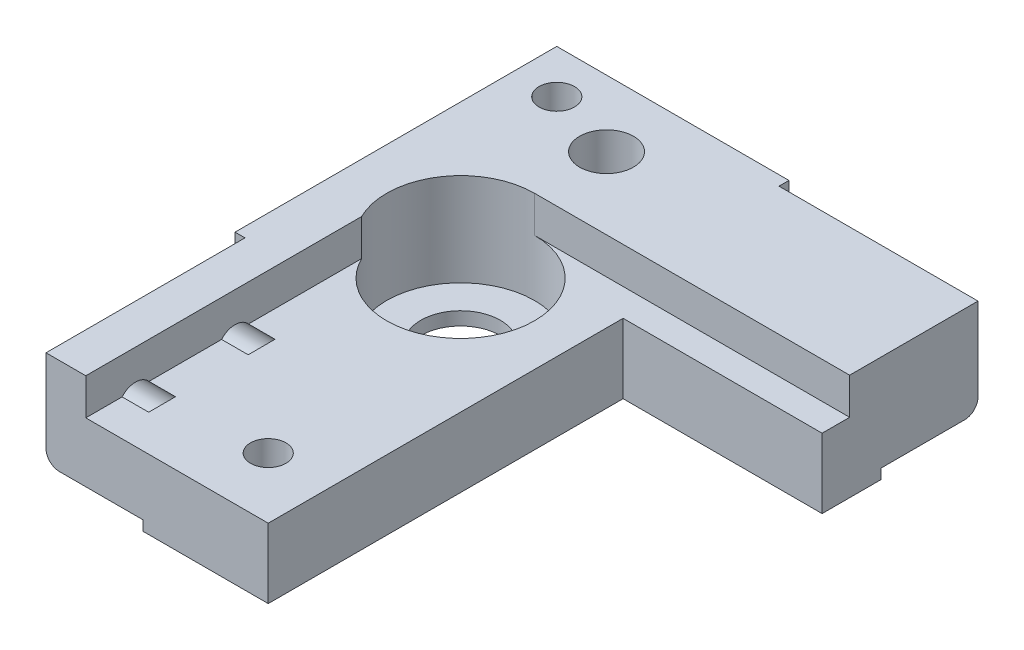
SolidWorks part; units mm, degrees
ref_plane "Alzado" through (0, 0, 0) normal (0, 0, 1) x (1, 0, 0)
ref_plane "Planta" through (0, 0, 0) normal (0, 1, 0) x (1, 0, 0)
ref_plane "Vista lateral" through (0, 0, 0) normal (1, 0, 0) x (0, 0, -1)
sketch "Croquis2" plane through (0, 0, 0) normal (0, 1, 0) x (-1, 0, 0)
  line L1 (0, 0) -> (-65, 0)
  line L2 (0, 0) -> (0, 78.5)
  line L3 (0, 78.5) -> (-35, 78.5)
  line L4 (-65, 0) -> (-65, 25)
  line L6 (-35, 78.5) -> (-35, 25)
  line L7 (-35, 25) -> (-65, 25)
  dimension "D1" = 78.5
  dimension "D2" = 35
  dimension "D3" = 65
  dimension "D4" = 25
extrude "Saliente-Extruir1" add sketch "Croquis2" along normal blind 16 separate body
sketch "Croquis6" plane through (0, 16, 0) normal (0, 1, 0) x (-1, 0, 0)
  line L5 (-65, 0) -> (0, 0) construction
  line L6 (-17.5, 32) -> (-17.5, 78.5) construction
  line L7 (0, 78.5) -> (-35, 78.5) construction
  circle A0 centre (-17.5, 32) radius 11.15
  dimension "D1" = 22.3
  dimension "D3" = 32
extrude "Cortar-Extruir4" cut sketch "Croquis6" against normal blind 14
sketch "Croquis22" plane through (0, 2, 0) normal (0, 1, 0) x (1, 0, 0)
  circle A0 centre (17.5, -32) radius 6
  dimension "D1" = 12
extrude "Cortar-Extruir17" cut sketch "Croquis22" against normal through all
sketch "Croquis8" plane through (0, 16, 0) normal (0, 1, 0) x (-1, 0, 0)
  line L8 (-65, 0) -> (0, 0) construction
  line L9 (0, 0) -> (0, 78.5) construction
  circle A3 centre (-17.5, 10) radius 4.05
  dimension "D1" = 8.1
  dimension "D2" = 10
  dimension "D3" = 17.5
extrude "Cortar-Extruir6" cut sketch "Croquis8" against normal through all
sketch "Croquis9" plane through (65, 0, 0) normal (1, 0, 0) x (0, 0, -1)
  line L0 (0, 16) -> (0, 0)
  line L1 (-25, 0) -> (0, 0) construction
  line L2 (0, 0) -> (-16, 0)
  line L3 (-16, 0) -> (-16, 1.4)
  line L4 (-16, 1.4) -> (-1.4, 1.4)
  line L5 (-1.4, 1.4) -> (-1.4, 16)
  line L6 (-1.4, 16) -> (0, 16)
  line L8 (0, 16) -> (0, 0) construction
  dimension "D1" = 16
  dimension "D2" = 16
  dimension "D3" = 1.4
sketch "Croquis17" plane through (65, 0, 0) normal (1, 0, 0) x (0, 0, -1)
  line L0 (-16.1, 0) -> (-16.1, 1.5)
  line L1 (-25, 0) -> (0, 0) construction
  line L2 (-16.1, 1.5) -> (-1.5, 1.5)
  line L3 (-1.5, 1.5) -> (-1.5, 16.1)
  line L4 (-1.5, 16.1) -> (0, 16.1)
  line L5 (0, 16) -> (0, 0) construction
  line L6 (0, 16.1) -> (0, 0)
  line L7 (0, 0) -> (-16.1, 0)
  line L8 (-1.4, 1.4) -> (-1.4, 16) construction
  line L9 (-1.4, 16) -> (0, 16) construction
  line L10 (-16, 1.4) -> (-1.4, 1.4) construction
  line L11 (-16, 0) -> (-16, 1.4) construction
  dimension "D1" = 0.1
  dimension "D2" = 0.1
  dimension "D3" = 0.1
  dimension "D4" = 0.1
extrude "Cortar-Extruir12" cut sketch "Croquis17" against normal blind 30
sketch "Croquis18" plane through (0, 0, 1.5) normal (0, 0, -1) x (-1, 0, 0)
  line L0 (-57.5, 8.75) -> (-42.5, 8.75) construction
  line L3 (-35, 16) -> (-35, 1.5) construction
  line L4 (-35, 8.75) -> (-42.5, 8.75) construction
  line L5 (-35, 16) -> (-65, 16) construction
  line L6 (-50, 16) -> (-50, 8.75) construction
  circle A0 centre (-42.5, 8.75) radius 2.675
  circle A1 centre (-57.5, 8.75) radius 2.675
  dimension "D1" = 5.35
  dimension "D2" = 15
extrude "Cortar-Extruir13" cut sketch "Croquis18" against normal blind 15
sketch "Croquis10" plane through (65, 0, 0) normal (1, 0, 0) x (0, 0, -1)
  line L0 (-25, 0) -> (-16.1, 0) construction
  line L1 (0, 16.1) -> (-16.1, 16.1)
  line L2 (0, 16.1) -> (0, 0)
  line L3 (0, 0) -> (-16.1, 0)
  line L4 (-16.1, 16.1) -> (-16.1, 0)
  line L5 (-16, 0) -> (-16, 1.4) construction
  line L6 (0, 16) -> (0, 0) construction
  line L7 (-1.4, 16) -> (0, 16) construction
  dimension "D1" = 0.1
  dimension "D2" = 0.1
sketch "Croquis11" plane through (0, 0, 78.5) normal (0, 0, 1) x (1, 0, 0)
  line L0 (0, 16) -> (0, 0)
  line L2 (0, 0) -> (16, 0)
  line L3 (0, 0) -> (35, 0) construction
  line L4 (16, 0) -> (16, 1.4)
  line L5 (16, 1.4) -> (1.4, 1.4)
  line L6 (1.4, 1.4) -> (1.4, 16)
  line L7 (1.4, 16) -> (0, 16)
  line L9 (0, 16) -> (0, 0) construction
  dimension "D1" = 1.4
  dimension "D2" = 16
  dimension "D3" = 16
sketch "Croquis15" plane through (0, 0, 78.5) normal (0, 0, 1) x (1, 0, 0)
  line L0 (0, 0) -> (0, 16.1)
  line L1 (0, 16.1) -> (1.5, 16.1)
  line L2 (1.5, 16.1) -> (1.5, 1.5)
  line L3 (1.5, 1.5) -> (16.1, 1.5)
  line L4 (16.1, 1.5) -> (16.1, 0)
  line L5 (0, 0) -> (35, 0) construction
  line L6 (16.1, 0) -> (0, 0)
  line L7 (1.4, 16) -> (0, 16) construction
  line L8 (1.4, 1.4) -> (1.4, 16) construction
  line L9 (16, 0) -> (16, 1.4) construction
  line L10 (16, 1.4) -> (1.4, 1.4) construction
  dimension "D1" = 0.1
  dimension "D2" = 0.1
  dimension "D3" = 0.1
  dimension "D4" = 0.1
extrude "Cortar-Extruir10" cut sketch "Croquis15" against normal blind 30
sketch "Croquis16" plane through (1.5, 0, 0) normal (-1, 0, 0) x (0, 0, 1)
  line L0 (56, 8.75) -> (48.5, 8.75) construction
  line L1 (48.5, 1.5) -> (48.5, 16) construction
  line L2 (56, 8.75) -> (71, 8.75) construction
  line L5 (78.5, 16) -> (48.5, 16) construction
  line L6 (63.5, 16) -> (63.5, 8.75) construction
  circle A0 centre (56, 8.75) radius 2.675
  circle A1 centre (71, 8.75) radius 2.675
  dimension "D1" = 5.35
  dimension "D2" = 15
sketch "Croquis12" plane through (0, 0, 78.5) normal (0, 0, 1) x (1, 0, 0)
  line L0 (1.4, 16) -> (0, 16) construction
  line L1 (0, 0) -> (16.1, 0)
  line L2 (0, 0) -> (0, 16.1)
  line L3 (0, 16.1) -> (16.1, 16.1)
  line L4 (16.1, 0) -> (16.1, 16.1)
  line L5 (16, 0) -> (16, 1.4) construction
  line L6 (0, 16) -> (0, 0) construction
  line L7 (0, 0) -> (16, 0) construction
  dimension "D1" = 0.1
  dimension "D2" = 0.1
extrude "Cortar-Extruir11" cut sketch "Croquis16" against normal blind 10
sketch "Croquis19" plane through (0, 16, 0) normal (0, 1, 0) x (1, 0, 0)
  line L0 (25.8455, -69.3455) -> (35, -69.3455) construction
  line L1 (35, -78.5) -> (35, -25) construction
  line L2 (6.5809, -6.5809) -> (0, -6.5809) construction
  line L3 (1.5, -78.5) -> (35, -78.5) construction
  line L4 (25.8455, -78.5) -> (25.8455, -69.3455) construction
  line L5 (0, 0) -> (0, -48.5) construction
  line L7 (35, 0) -> (0, 0) construction
  line L8 (6.5809, 0) -> (6.5809, -6.5809) construction
  circle A0 centre (6.5809, -6.5809) radius 2.675
  circle A1 centre (25.8455, -69.3455) radius 2.675
  dimension "D1" = 5.35
extrude "Cortar-Extruir14" cut sketch "Croquis19" against normal through all
sketch "Croquis23" plane through (0, 16, 0) normal (0, 1, 0) x (1, 0, 0)
  line L1 (35, -78.5) -> (7.5, -78.5)
  line L2 (35, -78.5) -> (35, -25)
  line L3 (17.5, -20.85) -> (65, -20.85)
  line L4 (7.5, -78.5) -> (7.5, -27.0682)
  line L6 (65, -25) -> (65, -1.5) construction
  line L7 (65, -20.85) -> (65, -25)
  line L8 (65, -25) -> (35, -25)
  arc A0 (17.5, -20.85) -> (7.5, -27.0682) centre (17.5, -32) ccw
  circle A1 centre (17.5, -32) radius 11.15 construction
  dimension "D1" = 27.5
extrude "Cortar-Extruir19" cut sketch "Croquis23" against normal blind 5.5
fillet "Redondeo1" radius 2 2 edges at (50, 1.5, 1.5) (1.5, 1.5, 63.5)
